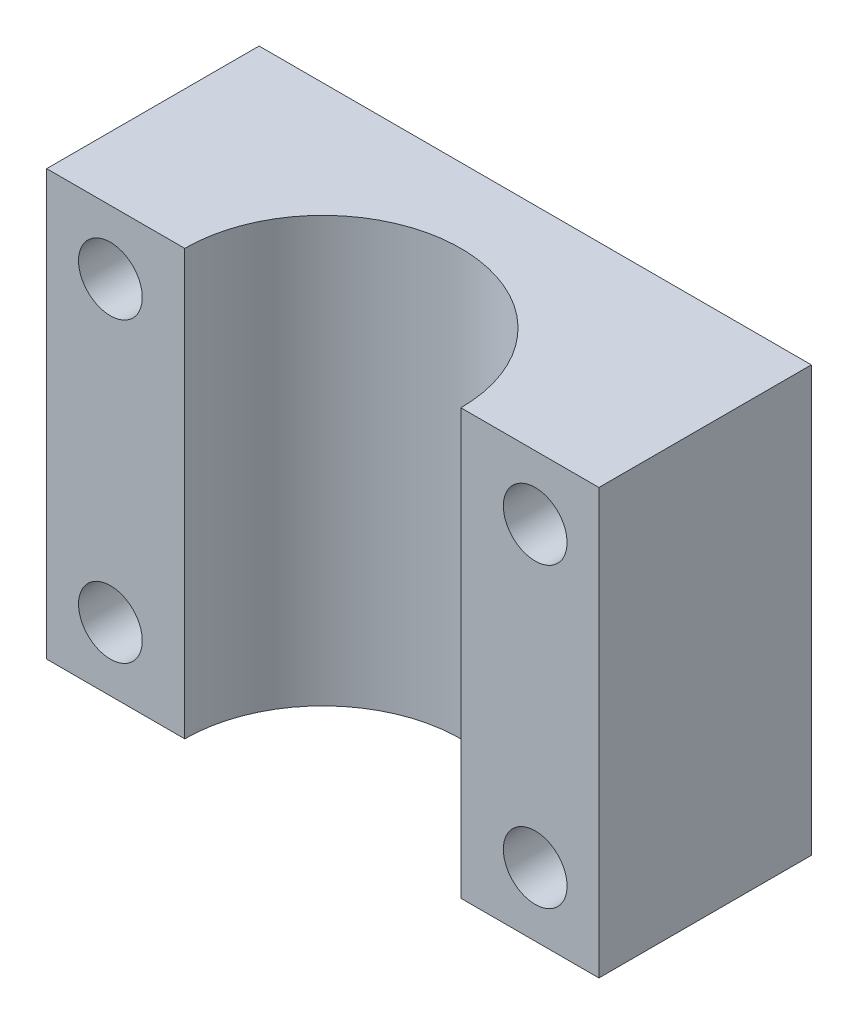
SolidWorks part; units mm, degrees
material "ABS"
ref_plane "Front Plane" through (0, 0, 0) normal (0, 0, 1) x (1, 0, 0)
ref_plane "Top Plane" through (0, 0, 0) normal (0, 1, 0) x (1, 0, 0)
ref_plane "Right Plane" through (0, 0, 0) normal (1, 0, 0) x (0, 0, -1)
sketch "Sketch1" plane through (0, 0, 0) normal (0, 1, 0) x (1, 0, 0)
  line L6 (0, 0) -> (26, 0)
  line L7 (0, 0) -> (0, 10)
  line L8 (0, 10) -> (26, 10)
  line L9 (26, 0) -> (26, 10)
extrude "Boss-Extrude1" add sketch "Sketch1" along normal blind 20
sketch "Sketch2" plane through (0, 20, 0) normal (0, 1, 0) x (1, 0, 0)
  line L1 (0, 0) -> (26, 0) construction
  line L2 (6.5, 0) -> (19.5, 0)
  arc A1 (19.5, 0) -> (6.5, 0) centre (13, 0) ccw
  dimension "D1" = 13
extrude "Cut-Extrude1" cut sketch "Sketch2" against normal through all
sketch "Sketch3" plane through (0, 0, -10) normal (0, 0, -1) x (-1, 0, 0)
  line L1 (-26, 0) -> (0, 0) construction
  line L2 (-26, 20) -> (-26, 0) construction
  line L3 (-26, 20) -> (0, 20) construction
  line L4 (0, 20) -> (0, 0) construction
  circle A0 centre (-23, 17) radius 1.5
  circle A1 centre (-3, 17) radius 1.5
  circle A2 centre (-3, 3) radius 1.5
  circle A3 centre (-23, 3) radius 1.5
  dimension "D1" = 3
  dimension "D2" = 3
  dimension "D3" = 3
  dimension "D4" = 3
extrude "Cut-Extrude2" cut sketch "Sketch3" against normal blind 10
